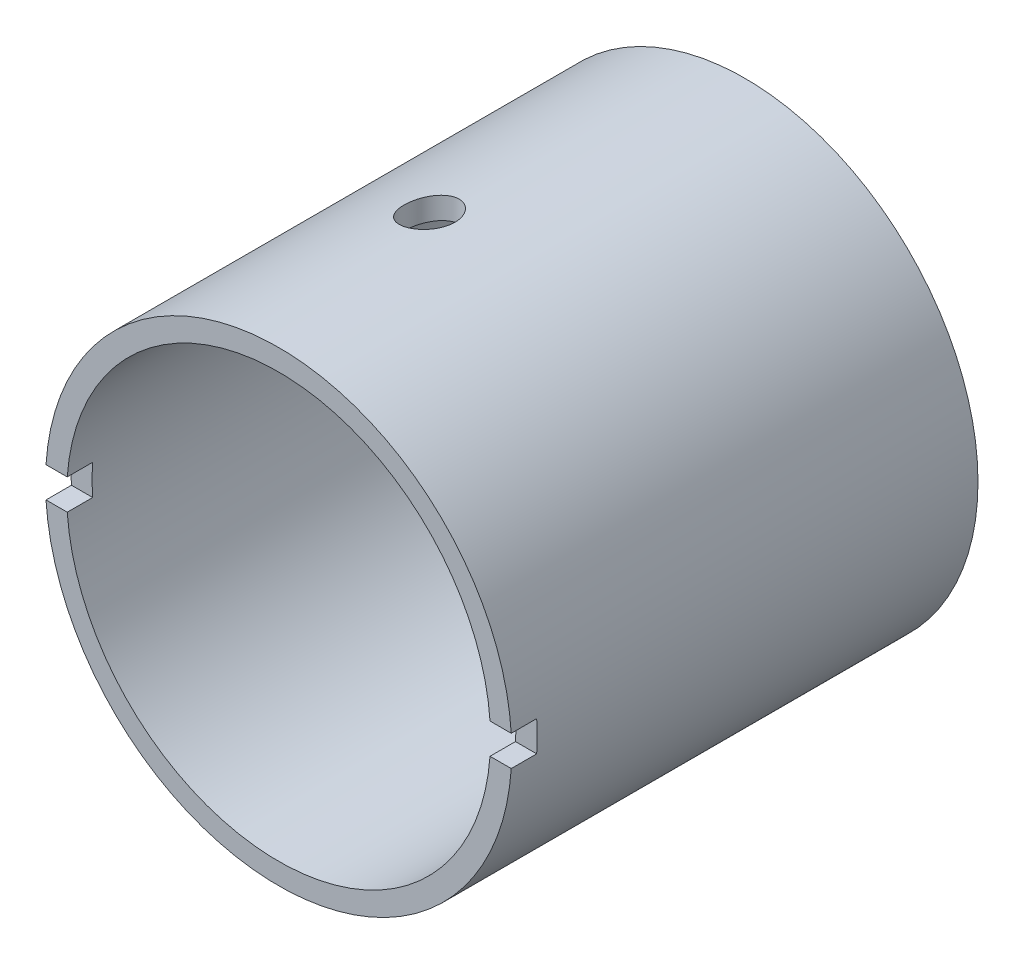
SolidWorks part; units mm, degrees
material "Glass"
ref_plane "Front Plane" through (0, 0, 0) normal (0, 0, 1) x (1, 0, 0)
ref_plane "Top Plane" through (0, 0, 0) normal (0, 1, 0) x (1, 0, 0)
ref_plane "Right Plane" through (0, 0, 0) normal (1, 0, 0) x (0, 0, -1)
sketch "Sketch1" plane through (0, 0, 0) normal (0, 0, 1) x (1, 0, 0)
  circle A0 centre (0, 0) radius 27.5
  circle A1 centre (0, 0) radius 25
  dimension "D1" = 55
  dimension "D2" = 2.5
extrude "Boss-Extrude1" add sketch "Sketch1" along normal blind 55
sketch "Sketch2" plane through (0, 0, 0) normal (0, 0, 1) x (1, 0, 0)
  line L0 (-20, 4.1) -> (-26.1241, 4.1)
  line L1 (-26.1241, 4.1) -> (-26.1241, -4.1)
  line L2 (-26.1241, -4.1) -> (-20, -4.1)
  line L3 (0, 4.1) -> (0, -4.1) construction
  line L4 (26.1241, -4.1) -> (20, -4.1)
  line L5 (26.1241, 4.1) -> (26.1241, -4.1)
  line L6 (20, 4.1) -> (26.1241, 4.1)
  circle A0 centre (-20, 0) radius 1.6
  arc A2 (-20, 4.1) -> (-20, -4.1) centre (-20, 0) cw
  arc A3 (20, 4.1) -> (20, -4.1) centre (20, 0) ccw
  circle A4 centre (20, 0) radius 1.6
  dimension "D1" = 3.2
  dimension "D4" = 2.5
  dimension "D2" = 20
extrude "Boss-Extrude2" add sketch "Sketch2" along normal blind 2
sketch "Sketch3" plane through (0, 0, 0) normal (0, 0, 1) x (1, 0, 0)
  line L1 (-29.0324, 1.8) -> (31.5033, 1.8)
  line L2 (-29.0324, 1.8) -> (-29.0324, -1.8)
  line L3 (-29.0324, -1.8) -> (31.5033, -1.8)
  line L4 (31.5033, 1.8) -> (31.5033, -1.8)
  point P4 (-29.0324, 0)
  dimension "D1" = 3.6
extrude "Cut-Extrude1" cut sketch "Sketch3" against normal blind 3 from surface at 55 starting at face at (27.5, 0, 55)
sketch "Sketch4" plane through (0, 0, 0) normal (0, 1, 0) x (1, 0, 0)
  line L0 (24.6615, 0) -> (-24.6615, 0) construction
  line L1 (0, -55) -> (0, 0) construction
  circle A0 centre (-5.5, -31.7) radius 3
  dimension "D3" = 6
  dimension "D1" = 31.7
  dimension "D2" = 5.5
extrude "Cut-Extrude2" cut sketch "Sketch4" along normal through all
